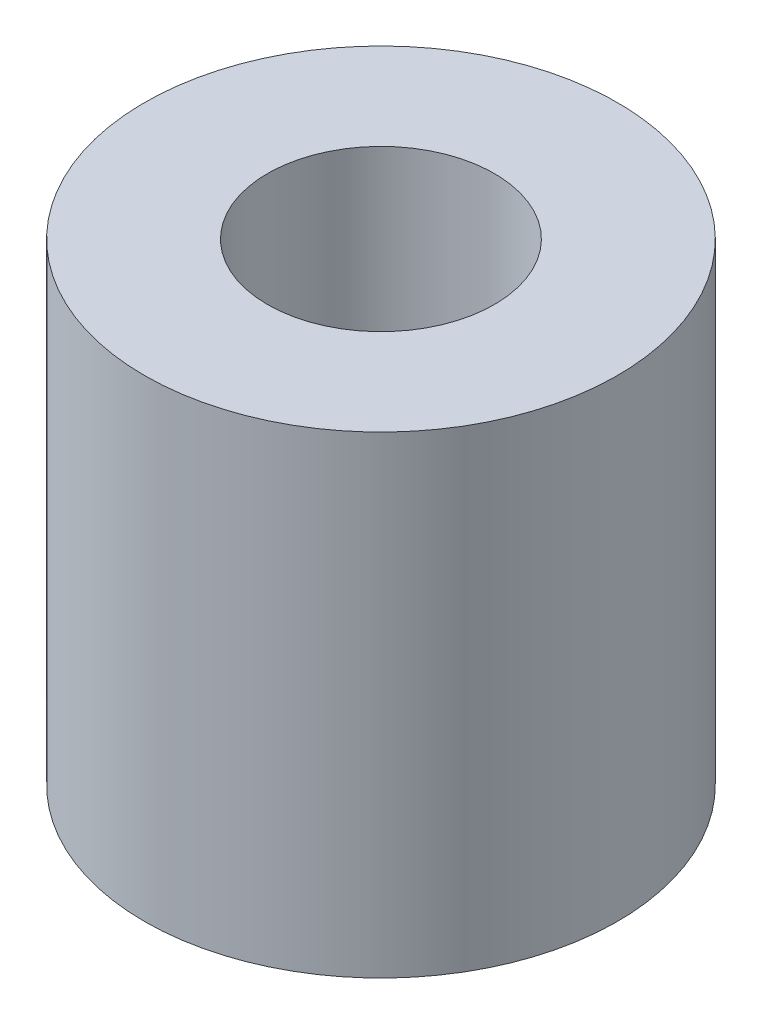
SolidWorks part; units mm, degrees
ref_plane "Front Plane" through (0, 0, 0) normal (0, 0, 1) x (1, 0, 0)
ref_plane "Top Plane" through (0, 0, 0) normal (0, 1, 0) x (1, 0, 0)
ref_plane "Right Plane" through (0, 0, 0) normal (1, 0, 0) x (0, 0, -1)
sketch "Sketch1" plane through (0, 0, 0) normal (0, 1, 0) x (1, 0, 0)
  circle A0 centre (0, 0) radius 3.175
  circle A1 centre (0, 0) radius 1.524
  dimension "D1" = 6.35
  dimension "D2" = 3.048
extrude "Extrude1" add sketch "Sketch1" along normal blind 6.35
